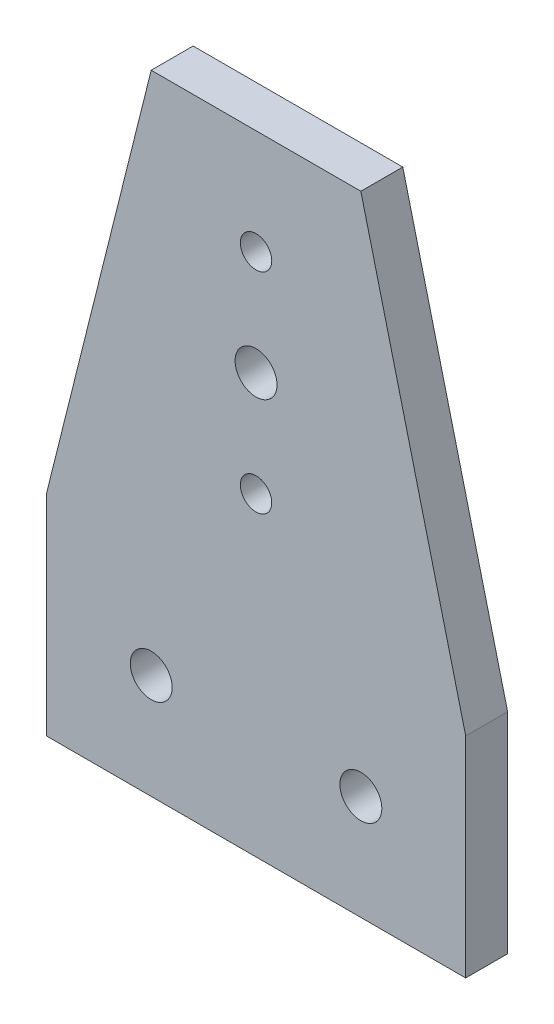
SolidWorks part; units mm, degrees
ref_plane "Plan de face" through (0, 0, 0) normal (0, 0, 1) x (1, 0, 0)
ref_plane "Plan de dessus" through (0, 0, 0) normal (0, 1, 0) x (1, 0, 0)
ref_plane "Plan de droite" through (0, 0, 0) normal (1, 0, 0) x (0, 0, -1)
sketch "Esquisse1" plane through (0, 0, 0) normal (0, 0, 1) x (1, 0, 0)
  line L0 (-63.6421, -47.6966) -> (16.3579, -47.6966)
  line L1 (16.3579, -47.6966) -> (16.3579, -7.6966)
  line L2 (16.3579, -7.6966) -> (-3.6421, 72.3034)
  line L3 (-3.6421, 72.3034) -> (-43.6421, 72.3034)
  line L4 (-43.6421, 72.3034) -> (-63.6421, -7.6966)
  line L5 (-63.6421, -7.6966) -> (-63.6421, -47.6966)
  line L6 (-23.6421, -47.6966) -> (-23.6421, 108.7079) construction
  dimension "D1" = 120
  dimension "D2" = 40
  dimension "D3" = 40
  dimension "D4" = 80
  dimension "D5" = 20
extrude "Boss.-Extru.1" add sketch "Esquisse1" along normal blind 8
sketch "Esquisse2" plane through (0, 0, 8) normal (0, 0, 1) x (1, 0, 0)
  line L0 (-23.6421, 72.3034) -> (-23.6421, -47.6966) construction
  line L1 (-3.6421, 72.3034) -> (-43.6421, 72.3034) construction
  line L2 (-63.6421, -47.6966) -> (16.3579, -47.6966) construction
  line L3 (-63.6421, -27.6966) -> (16.3579, -27.6966) construction
  line L4 (-63.6421, -7.6966) -> (-63.6421, -47.6966) construction
  line L5 (16.3579, -47.6966) -> (16.3579, -7.6966) construction
  circle A0 centre (-23.6421, 52.3034) radius 3
  circle A1 centre (-23.6421, 32.3034) radius 4
  circle A2 centre (-23.6421, 12.3034) radius 3
  circle A3 centre (-43.6421, -27.6966) radius 4
  circle A4 centre (-3.6421, -27.6966) radius 4
  dimension "D1" = 8
  dimension "D2" = 8
  dimension "D4" = 40
  dimension "D5" = 20
  dimension "D6" = 40
  dimension "D7" = 20
  dimension "D8" = 6
  dimension "D9" = 6
  dimension "D10" = 8
  dimension "D3" = 20
extrude "Enlèv. mat.-Extru.1" cut sketch "Esquisse2" against normal through all
